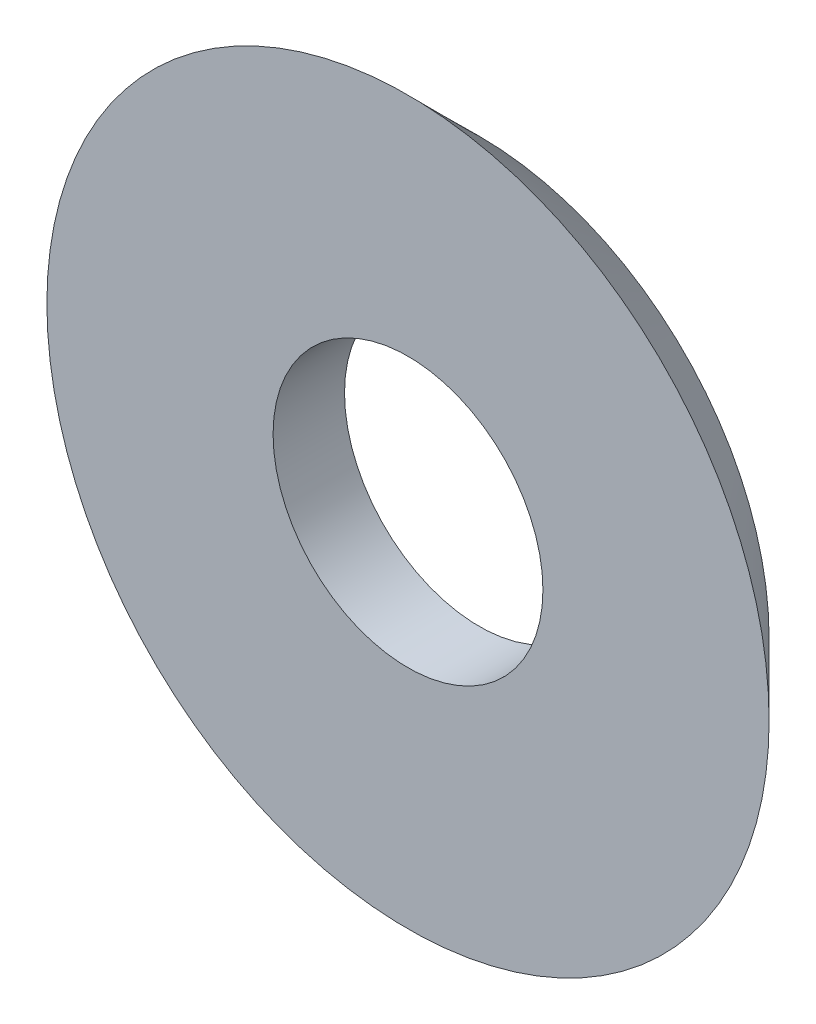
SolidWorks part; units mm, degrees
ref_plane "Front" through (0, 0, 0) normal (0, 0, 1) x (1, 0, 0)
ref_plane "Top" through (0, 0, 0) normal (0, 1, 0) x (1, 0, 0)
ref_plane "Right" through (0, 0, 0) normal (1, 0, 0) x (0, 0, -1)
sketch "Sketch1" plane through (0, 0, 0) normal (0, 1, 0) x (1, 0, 0)
  line L0 (7.3, 0) -> (9.1, 0)
  line L1 (0, 0) -> (7.3, 0)
  line L2 (0, 0) -> (0, 1.8)
  line L3 (0, 1.8) -> (7.3, 1.8)
  line L4 (7.3, 0) -> (7.3, 1.8)
  line L5 (9.1, 0) -> (7.3, 1.8)
  line L6 (3.4, 1.8) -> (3.4, 0)
  dimension "D1" = 45
  dimension "D2" = 7.3
  dimension "D3" = 1.8
  dimension "D4" = 3.4
revolve "Revolve1" add sketch "Sketch1" angle 360 about L2
